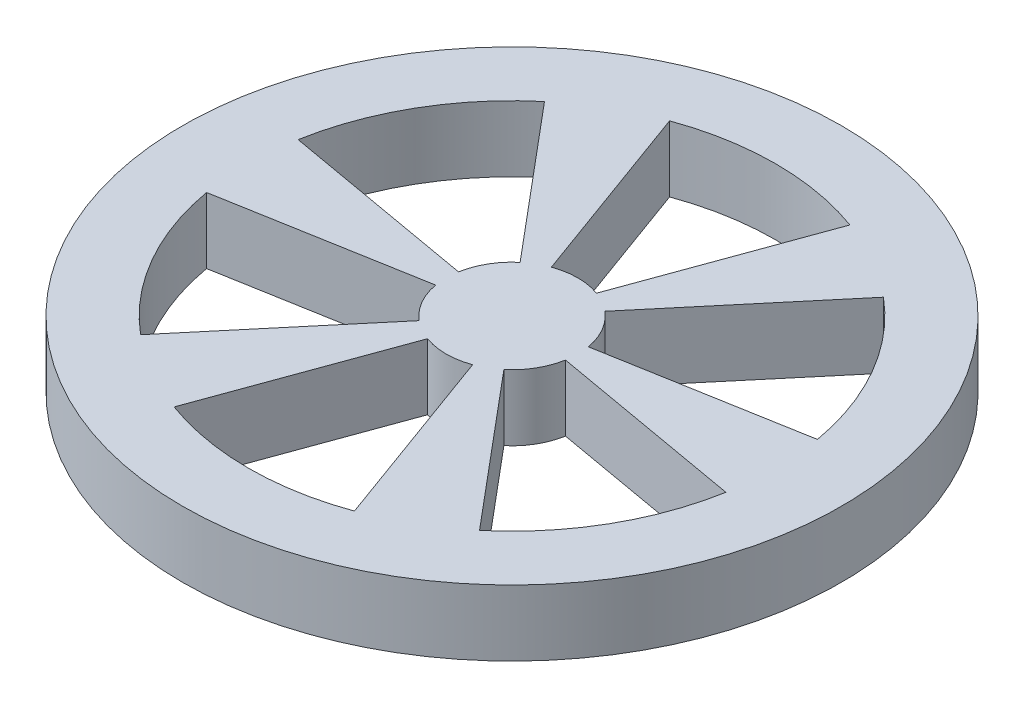
SolidWorks part; units mm, degrees
material "5052-H38"
ref_plane "Front" through (0, 0, 0) normal (0, 0, 1) x (1, 0, 0)
ref_plane "Top" through (0, 0, 0) normal (0, 1, 0) x (1, 0, 0)
ref_plane "Right" through (0, 0, 0) normal (1, 0, 0) x (0, 0, -1)
sketch "ｽｹｯﾁ1" plane through (0, 0, 0) normal (0, 1, 0) x (1, 0, 0)
  line L0 (-3.4202, 9.3969) -> (-13.6808, 37.5877)
  line L1 (3.4202, 9.3969) -> (13.6808, 37.5877)
  line L2 (0, 0) -> (0, 40) construction
  line L3 (6.4284, 7.6613) -> (25.712, 30.6426)
  line L4 (9.8486, 1.7373) -> (39.3928, 6.9468)
  line L5 (9.8496, -1.7356) -> (39.3938, -6.9451)
  line L6 (6.4294, -7.6596) -> (25.713, -30.6409)
  line L7 (3.4222, -9.3969) -> (13.6828, -37.5877)
  line L8 (-3.4182, -9.3969) -> (-13.6788, -37.5877)
  line L9 (-6.4264, -7.6613) -> (-25.71, -30.6426)
  line L10 (-9.8466, -1.7373) -> (-39.3908, -6.9468)
  line L11 (-9.8476, 1.7356) -> (-39.3918, 6.9451)
  line L12 (-6.4274, 7.6596) -> (-25.711, 30.6409)
  circle A0 centre (0, 0) radius 50
  arc A1 (3.4202, 9.3969) -> (-3.4202, 9.3969) centre (0, 0) ccw
  arc A2 (13.6808, 37.5877) -> (-13.6808, 37.5877) centre (0, 0) ccw
  arc A3 (39.3928, 6.9468) -> (25.712, 30.6426) centre (0.0005, 0.0009) ccw
  arc A4 (9.8486, 1.7373) -> (6.4284, 7.6613) centre (0.0005, 0.0009) ccw
  arc A5 (25.713, -30.6409) -> (39.3938, -6.9451) centre (0.0015, 0.0009) ccw
  arc A6 (6.4294, -7.6596) -> (9.8496, -1.7356) centre (0.0015, 0.0009) ccw
  arc A7 (-13.6788, -37.5877) -> (13.6828, -37.5877) centre (0.002, 0) ccw
  arc A8 (-3.4182, -9.3969) -> (3.4222, -9.3969) centre (0.002, 0) ccw
  arc A9 (-39.3908, -6.9468) -> (-25.71, -30.6426) centre (0.0015, -0.0009) ccw
  arc A10 (-9.8466, -1.7373) -> (-6.4264, -7.6613) centre (0.0015, -0.0009) ccw
  arc A11 (-25.711, 30.6409) -> (-39.3918, 6.9451) centre (0.0005, -0.0009) ccw
  arc A12 (-6.4274, 7.6596) -> (-9.8476, 1.7356) centre (0.0005, -0.0009) ccw
  point P35 (0.001, 0)
  dimension "D1" = 100
  dimension "D2" = 20
  dimension "D3" = 80
  dimension "D4" = 20
  dimension "D5" = 20
  dimension "D6" = 6
extrude "ﾎﾞｽ - 押し出し1" add sketch "ｽｹｯﾁ1" along normal blind 10
